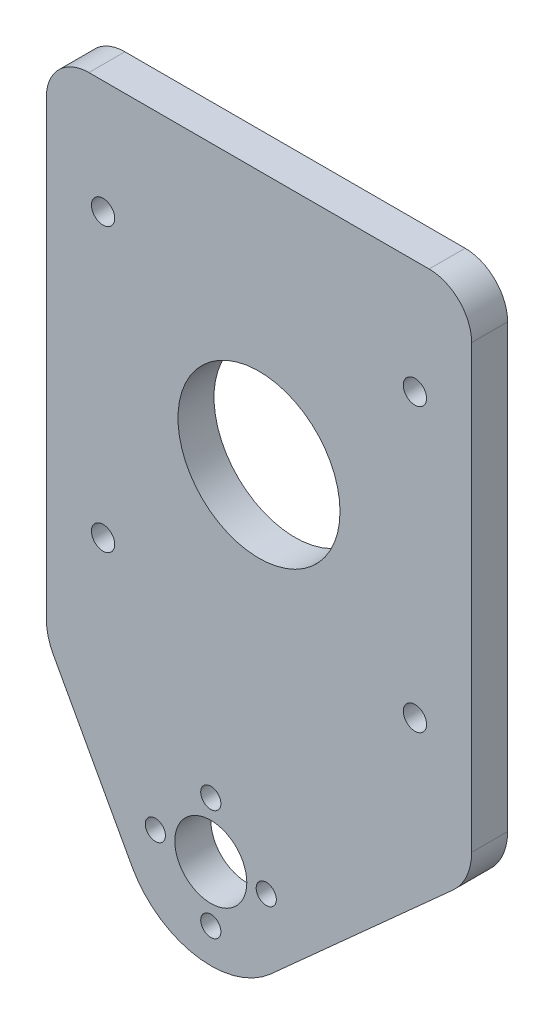
SolidWorks part; units mm, degrees
ref_plane "Front Plane" through (0, 0, 0) normal (0, 0, 1) x (1, 0, 0)
ref_plane "Top Plane" through (0, 0, 0) normal (0, 1, 0) x (1, 0, 0)
ref_plane "Right Plane" through (0, 0, 0) normal (1, 0, 0) x (0, 0, -1)
sketch "Sketch1" plane through (0, 0, 0) normal (0, 0, 1) x (1, 0, 0)
  line L1 (0, 0) -> (304.8, 0)
  line L2 (0, 0) -> (0, 89.8)
  line L3 (0, 89.8) -> (304.8, 89.8)
  line L4 (304.8, 0) -> (304.8, 89.8)
  circle A3 centre (152.4, 44.9) radius 14.2875
  point P7 (152.4, 44.9)
  circle B0 centre (109.4016, 62.8594) radius 2.54
  circle B1 centre (109.3994, 26.9384) radius 2.54
  circle B2 centre (73.4784, 26.9406) radius 2.54
  circle B3 centre (73.4806, 62.8616) radius 2.54
  circle B4 centre (91.44, 44.9) radius 17.145
  circle B5 centre (195.4006, 62.8616) radius 2.54
  circle B6 centre (231.3216, 62.8594) radius 2.54
  circle B7 centre (231.3194, 26.9384) radius 2.54
  circle B8 centre (195.3984, 26.9406) radius 2.54
  circle B9 centre (213.36, 44.9) radius 17.145
  dimension "D3" = 60.96
  dimension "D4" = 60.96
  dimension "D6" = 28.575
  dimension "D1" = 89.8
  dimension "D2" = 304.8
sketch_block_instance "Block1-1"
sketch_block "Block1" parameters "D1"=5.08, "D2"=34.29
sketch_block_instance "Block2-1"
sketch_block "Block2" parameters "D1"=5.08, "D2"=34.29
extrude "Boss-Extrude1" add sketch "Sketch1" along normal blind 6.35
sketch "Sketch2" plane through (0, 0, 6.35) normal (0, 0, 1) x (1, 0, 0)
  line L0 (304.8, 89.8) -> (0, 89.8) construction
  line L1 (114.9, 0) -> (189.9, 0)
  line L2 (114.9, 0) -> (114.9, 89.8)
  line L3 (114.9, 89.8) -> (189.9, 89.8)
  line L4 (189.9, 0) -> (189.9, 89.8)
  line L5 (114.9, 0) -> (189.9, 89.8) construction
  line L6 (114.9, 89.8) -> (189.9, 0) construction
  line L8 (114.9, 89.8) -> (-29.3949, 89.8)
  line L9 (114.9, 89.8) -> (114.9, -10.172)
  line L10 (114.9, -10.172) -> (-29.3949, -10.172)
  line L11 (-29.3949, 89.8) -> (-29.3949, -10.172)
  line L12 (189.9, 89.8) -> (343.3103, 89.8)
  line L13 (189.9, 89.8) -> (189.9, -29.3261)
  line L14 (189.9, -29.3261) -> (343.3103, -29.3261)
  line L15 (343.3103, 89.8) -> (343.3103, -29.3261)
  point P0 (152.4, 44.9)
  line M1 (0, 89.8) -> (0, 0)
  line M2 (0, 0) -> (304.8, 0)
  line M3 (304.8, 0) -> (304.8, 89.8)
  line M4 (304.8, 89.8) -> (0, 89.8)
  circle M6 centre (91.44, 44.9) radius 17.145
  circle M7 centre (109.4016, 62.8594) radius 2.54
  circle M8 centre (109.3994, 26.9384) radius 2.54
  circle M9 centre (73.4784, 26.9406) radius 2.54
  circle M10 centre (73.4806, 62.8616) radius 2.54
  circle M11 centre (213.36, 44.9) radius 17.145
  circle M12 centre (195.4006, 62.8616) radius 2.54
  circle M13 centre (231.3216, 62.8594) radius 2.54
  circle M14 centre (231.3194, 26.9384) radius 2.54
  circle M15 centre (195.3984, 26.9406) radius 2.54
  dimension "D1" = 75
extrude "Cut-Extrude1" cut sketch "Sketch2" against normal blind 10 contours L4 M2 M3 M4 M11 M13 M15 M14 M12 | L2 M2 M4 M1 M6 M8 M10 M9 M7
sketch "Sketch4" plane through (0, 0, 6.35) normal (0, 0, 1) x (1, 0, 0)
  line L0 (114.9, 0) -> (189.9, 0) construction
  line L1 (189.9, 0) -> (154.512, -31.8068)
  line L2 (114.9, 0) -> (129.9651, -27.6048)
  line L3 (189.9, 0) -> (114.9, 0)
  line L4 (189.9, 0) -> (189.9, 89.8) construction
  arc A2 (129.9651, -27.6048) -> (154.512, -31.8068) centre (143.9, -20) ccw
  circle A3 centre (143.9, -20) radius 6.35
  circle A4 centre (143.9, -29.779) radius 1.778
  circle A5 centre (134.121, -20) radius 1.778
  circle A6 centre (153.679, -20) radius 1.778
  circle A7 centre (143.9, -10.221) radius 1.778
  dimension "D1" = 46
  dimension "D3" = 31.75
  dimension "D4" = 20
  dimension "D5" = 12.7
  dimension "D6" = 3.556
  dimension "D7" = 3.556
  dimension "D8" = 3.556
  dimension "D9" = 3.556
extrude "Boss-Extrude2" add sketch "Sketch4" against normal up to surface (6.35 mm away) up to face at (166.6875, 44.9, 0)
fillet "Fillet1" radius 10 2 edges at (114.9, 0, 3.175) (189.9, 0, 3.175)
fillet "Fillet2" radius 7.5 2 edges at (114.9, 89.8, 3.175) (189.9, 89.8, 3.175)
sketch "Sketch7" plane through (0, 0, 6.35) normal (0, 0, 1) x (1, 0, 0)
  line L1 (182.4, 89.8) -> (122.4, 89.8) construction
  line L2 (189.9, 4.4576) -> (189.9, 82.3) construction
  line L3 (114.9, 2.5511) -> (114.9, 82.3) construction
  line L4 (166.6875, 44.9) -> (152.4, 44.9) construction
  circle A0 centre (179.9, 69.8) radius 2.05
  circle A1 centre (124.9, 69.8) radius 2.05
  circle A4 centre (152.4, 44.9) radius 14.2875 construction
  circle A5 centre (124.9, 20) radius 2.05
  circle A6 centre (179.9, 20) radius 2.05
  dimension "D1" = 4.1
  dimension "D2" = 4.1
  dimension "D3" = 20
  dimension "D4" = 20
  dimension "D5" = 10
  dimension "D6" = 10
extrude "Cut-Extrude2" cut sketch "Sketch7" against normal blind 10
scale "Scale1" scale about centroid uniform scaling yes scale factor 0.333333
